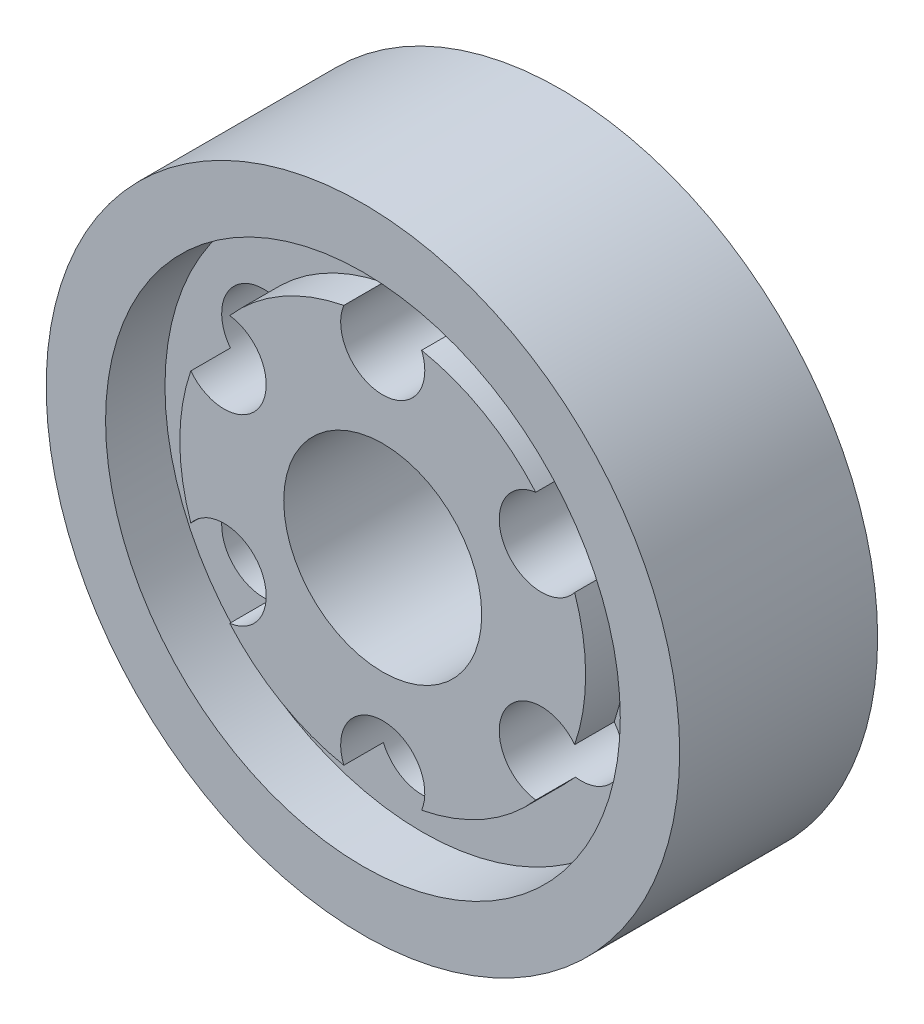
SolidWorks part; units mm, degrees
material "201 Annealed Stainless Steel (SS)"
ref_plane "Front" through (0, 0, 0) normal (0, 0, 1) x (1, 0, 0)
ref_plane "Top" through (0, 0, 0) normal (0, 1, 0) x (1, 0, 0)
ref_plane "Right" through (0, 0, 0) normal (1, 0, 0) x (0, 0, -1)
sketch "Sketch1" plane through (0, 0, 0) normal (0, 0, 1) x (1, 0, 0)
  circle A0 centre (0, 0) radius 32
  dimension "D1" = 64
extrude "Boss-Extrude1" add sketch "Sketch1" along normal blind 20
sketch "Sketch2" plane through (0, 0, 20) normal (0, 0, 1) x (1, 0, 0)
  circle A0 centre (0, 0) radius 26
  dimension "D1" = 52
extrude "Cut-Extrude1" cut sketch "Sketch2" against normal blind 6
sketch "Sketch3" plane through (0, 0, 14) normal (0, 0, 1) x (1, 0, 0)
  circle A0 centre (0, 0) radius 20.5
  dimension "D1" = 41
extrude "Boss-Extrude2" add sketch "Sketch3" along normal blind 4
sketch "Sketch4" plane through (0, 0, 18) normal (0, 0, 1) x (1, 0, 0)
  circle A0 centre (0, 0) radius 10
  dimension "D1" = 20
extrude "Cut-Extrude2" cut sketch "Sketch4" against normal blind 82
sketch "Sketch5" plane through (0, 0, 18) normal (0, 0, 1) x (1, 0, 0)
  circle A0 centre (0, 18.5) radius 4.25
  circle A1 centre (0, 0) radius 10 construction
  dimension "D1" = 8.5
  dimension "D2" = 4.25
extrude "Cut-Extrude3" cut sketch "Sketch5" against normal through all
pattern_circular "CirPattern1" count 6 every 60 about axis through (0, 0, 0) along (0, 0, 1) of "Cut-Extrude3"
